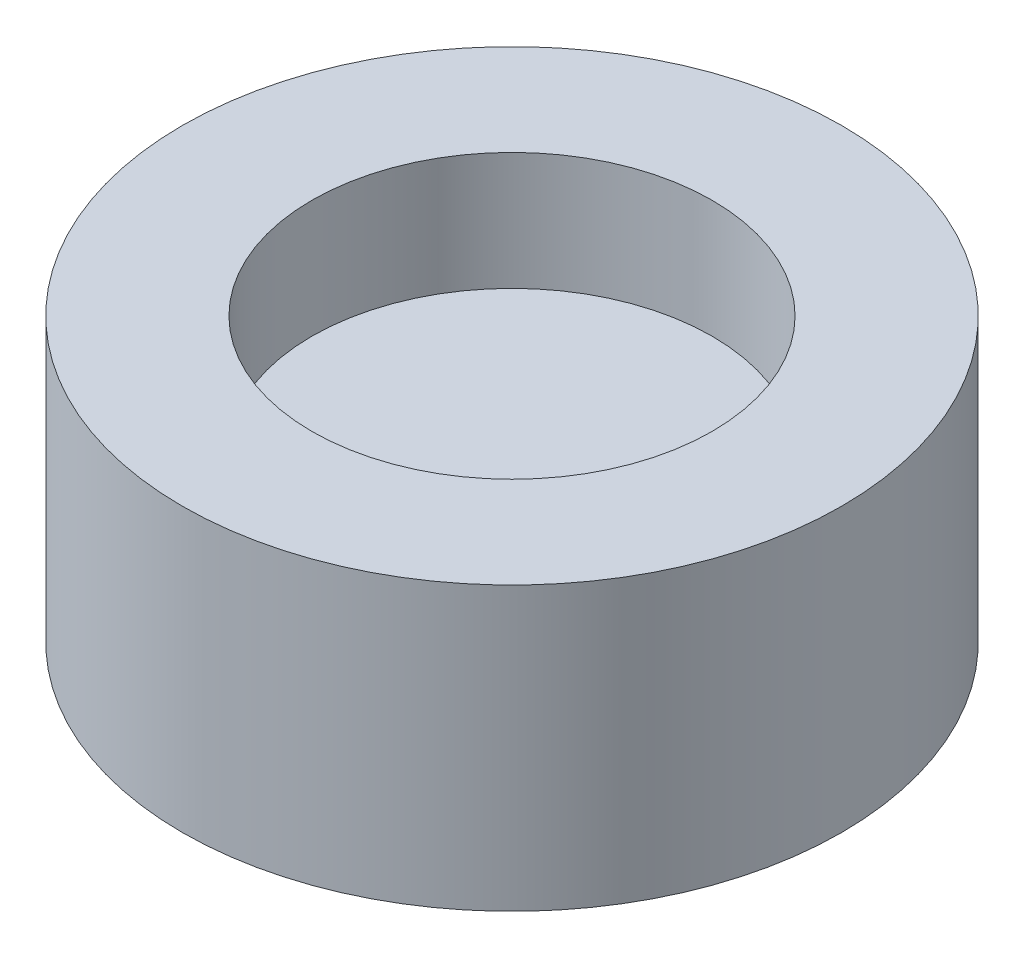
SolidWorks part; units mm, degrees
ref_plane "Front Plane" through (0, 0, 0) normal (0, 0, 1) x (1, 0, 0)
ref_plane "Top Plane" through (0, 0, 0) normal (0, 1, 0) x (1, 0, 0)
ref_plane "Right Plane" through (0, 0, 0) normal (1, 0, 0) x (0, 0, -1)
sketch "Sketch1" plane through (0, 0, 0) normal (0, 1, 0) x (1, 0, 0)
  circle A0 centre (0, 0) radius 5.25
  circle A1 centre (0, 0) radius 7
  dimension "D1" = 10.5
  dimension "D2" = 14
extrude "Boss-Extrude1" add sketch "Sketch1" along normal blind 2.5
sketch "Sketch2" plane through (0, 2.5, 0) normal (0, 1, 0) x (1, 0, 0)
  circle A0 centre (0, 0) radius 7
extrude "Boss-Extrude2" add sketch "Sketch2" along normal blind 1
sketch "Sketch3" plane through (0, 3.5, 0) normal (0, 1, 0) x (1, 0, 0)
  circle A0 centre (0, 0) radius 4.25
  circle A1 centre (0, 0) radius 7
  dimension "D1" = 8.5
extrude "Boss-Extrude3" add sketch "Sketch3" along normal blind 2.5
